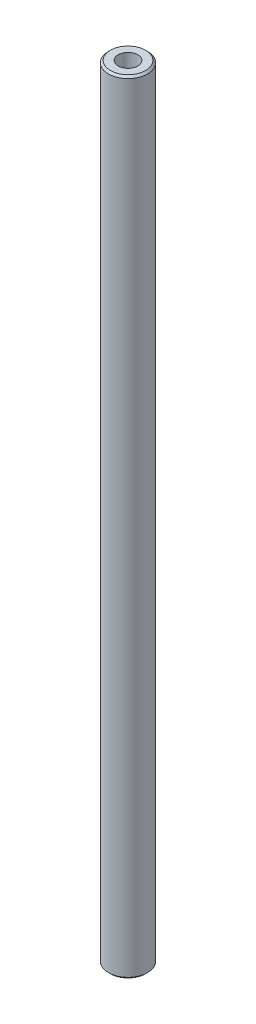
SolidWorks part; units mm, degrees
ref_plane "Face" through (0, 0, 0) normal (0, 0, 1) x (1, 0, 0)
ref_plane "Dessus" through (0, 0, 0) normal (0, 1, 0) x (1, 0, 0)
ref_plane "Droite" through (0, 0, 0) normal (1, 0, 0) x (0, 0, -1)
sketch "Esquisse1" plane through (0, 0, 0) normal (0, 1, 0) x (1, 0, 0)
  circle A0 centre (0, 0) radius 5
  dimension "D1" = 10
extrude "Extrusion1" add sketch "Esquisse1" along normal blind 200
chamfer "Chanfrein1" distance 0.5 angle 45 2 edges at (0, 200, 5) (0, 0, 5)
sketch "Esquisse2" plane through (0, 0, 0) normal (0, -1, 0) x (1, 0, 0)
  circle A0 centre (0, 0) radius 2.5
  dimension "D1" = 5
extrude "Extrusion2" cut sketch "Esquisse2" against normal blind 15
sketch "Esquisse3" plane through (0, 200, 0) normal (0, 1, 0) x (1, 0, 0)
  circle A0 centre (0, 0) radius 2.5
  dimension "D1" = 5
extrude "Extrusion3" cut sketch "Esquisse3" against normal blind 15
